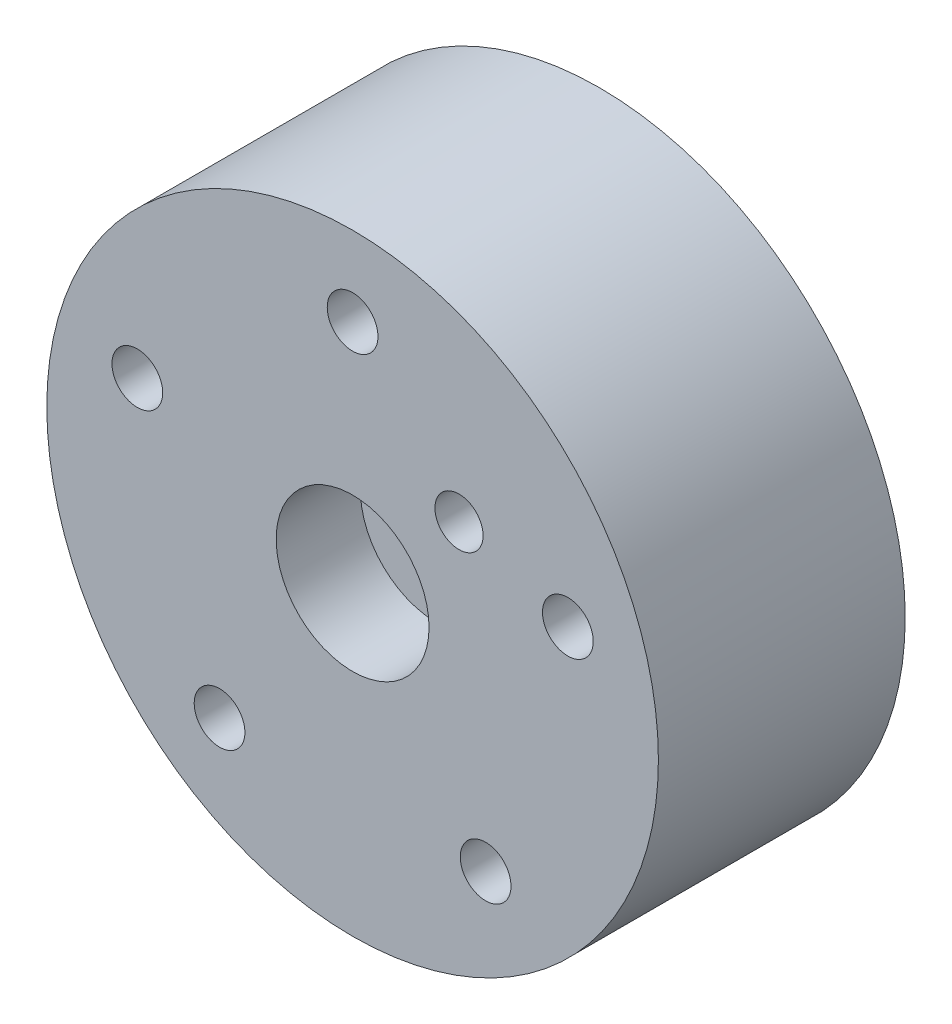
SolidWorks part; units mm, degrees
ref_plane "Front" through (0, 0, 0) normal (0, 0, 1) x (1, 0, 0)
ref_plane "Top" through (0, 0, 0) normal (0, 1, 0) x (1, 0, 0)
ref_plane "Right" through (0, 0, 0) normal (1, 0, 0) x (0, 0, -1)
sketch "Sketch1" plane through (0, 0, 0) normal (0, 0, 1) x (1, 0, 0)
  line L0 (-59.5, 57) -> (59.5, 57)
  line L1 (59.5, 57) -> (59.5, -57)
  line L2 (-59.5, 57) -> (-59.5, -57)
  line L3 (-59.5, -57) -> (59.5, -57)
  line L4 (-59.5, 57) -> (59.5, -57) construction
  point P3 (0, 0)
extrude "Boss-Extrude1" add sketch "Sketch1" along normal blind 41
sketch "Sketch4" plane through (0, 0, 0) normal (0, 0, -1) x (-1, 0, 0)
  line L0 (0, 0) -> (0, 37.6) construction
  circle A0 centre (0, 37.6) radius 4.2145
  circle A1 centre (35.7597, 11.619) radius 4.2145
  circle A2 centre (22.1007, -30.419) radius 4.2145
  circle A3 centre (-22.1007, -30.419) radius 4.2145
  circle A4 centre (-35.7597, 11.619) radius 4.2145
  point P16 (0, 0)
  dimension "D1" = 5
  dimension "D2" = 37.6
extrude "Cut-Extrude1" cut sketch "Sketch4" against normal blind 41
sketch "Sketch7" plane through (0, 0, 0) normal (0, 0, -1) x (-1, 0, 0)
  line L0 (0, 0) -> (0, 37.6) construction
  line L1 (0, 0) -> (35.7597, 11.619) construction
  line L2 (0, 0) -> (22.1007, -30.419) construction
  line L3 (0, 0) -> (-22.1007, -30.419) construction
  line L4 (0, 0) -> (-35.7597, 11.619) construction
  circle A0 centre (0, 37.6) radius 7
  circle A1 centre (0, 37.6) radius 4.2145 construction
  circle A2 centre (35.7597, 11.619) radius 7
  circle A3 centre (22.1007, -30.419) radius 7
  circle A4 centre (-22.1007, -30.419) radius 7
  circle A5 centre (-35.7597, 11.619) radius 7
  circle A6 centre (0, 0) radius 37.6 construction
  point P17 (0, 0)
  dimension "D2" = 14
  dimension "D1" = 37.6
  dimension "D3" = 5
extrude "Cut-Extrude2" cut sketch "Sketch7" against normal blind 35
sketch "Sketch8" plane through (0, 0, 0) normal (0, 0, -1) x (-1, 0, 0)
  line L0 (0, 0) -> (-17.6777, 17.6777) construction
  circle A0 centre (-17.6777, 17.6777) radius 4
  circle A1 centre (0, 0) radius 25 construction
  dimension "D1" = 25
extrude "Cut-Extrude3" cut sketch "Sketch8" against normal blind 55
sketch "Sketch9" plane through (0, 0, 41) normal (0, 0, 1) x (1, 0, 0)
  circle A0 centre (0, 0) radius 12.7
extrude "Cut-Extrude4" cut sketch "Sketch9" against normal blind 14
sketch "Sketch10" plane through (0, 0, 0) normal (0, 0, -1) x (-1, 0, 0)
  circle A0 centre (0, 0) radius 50.8
extrude "Cut-Extrude5" cut sketch "Sketch10" against normal blind 55 flip side to cut
